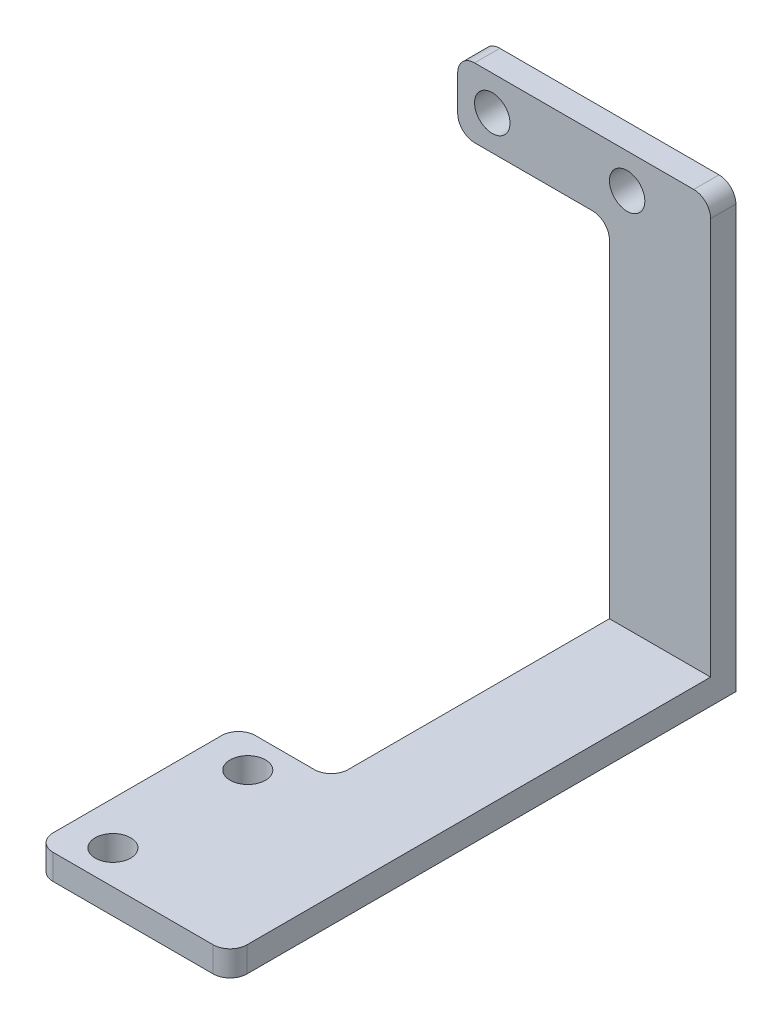
SolidWorks part; units mm, degrees
ref_plane "Front Plane" through (0, 0, 0) normal (0, 0, 1) x (1, 0, 0)
ref_plane "Top Plane" through (0, 0, 0) normal (0, 1, 0) x (1, 0, 0)
ref_plane "Right Plane" through (0, 0, 0) normal (1, 0, 0) x (0, 0, -1)
sketch "Sketch1" plane through (0, 0, 0) normal (0, 1, 0) x (1, 0, 0)
  line L0 (-17, -45) -> (6, -45) construction
  line L5 (-6, 0) -> (6, 0)
  line L6 (-6, 0) -> (-6, -33)
  line L8 (6, 0) -> (6, -57)
  line L9 (6, -57) -> (-17, -57)
  line L11 (-6, -33) -> (-17, -33)
  line L12 (-17, -57) -> (-17, -33)
  circle A4 centre (-11.9, -37) radius 2.1
  circle A5 centre (-11.9, -53) radius 2.1
  point P2 (0, 0)
  dimension "D2" = 4.2
  dimension "D1" = 24
  dimension "D3" = 16
  dimension "D4" = 3
  dimension "D5" = 11
  dimension "D6" = 12
  dimension "D7" = 45
extrude "Boss-Extrude1" add sketch "Sketch1" along normal blind 3
sketch "Sketch2" plane through (0, 0, 0) normal (0, 0, 1) x (1, 0, 0)
  line L0 (-11.9, 52.1) -> (-11.9, 43.9) construction
  line L1 (6, 0) -> (-6, 0)
  line L2 (6, 0) -> (6, 52.1)
  line L4 (-6, 0) -> (-6, 43.9)
  line L5 (6, 52.1) -> (-24, 52.1)
  line L7 (-6, 43.9) -> (-24, 43.9)
  line L8 (-24, 52.1) -> (-24, 43.9)
  line L11 (-17, 3) -> (6, 3) construction
  circle A0 centre (-19.9, 48) radius 2.1
  circle A1 centre (-3.9, 48) radius 2.1
  dimension "D1" = 4.2
  dimension "D2" = 16
  dimension "D4" = 2
  dimension "D5" = 2
  dimension "D6" = 2
  dimension "D3" = 45
extrude "Boss-Extrude2" add sketch "Sketch2" against normal blind 3
fillet "Fillet1" radius 2 8 edges at (-6, 1.5, 33) (6, 52.1, -1.5) (-24, 52.1, -1.5) (-24, 43.9, -1.5) (-6, 43.9, -1.5) (6, 1.5, 57) (-17, 1.5, 33) (-17, 1.5, 57)
equation "\"width\"= 24"
equation "\"thk\"= 3"
equation "\"holesize\"= 4.2"
equation "\"holedistance\"= ( 20 + 12 ) / 2"
equation "\"threaded_hole\"= 3.9"
equation "\"fillet_radius\"= 2"
equation "\"ground_clearance\"= 25"
equation "\"tire_thk\"= 4"
equation "\"innerwheel_diam\" = \"wheel_diam\"-2*\"tire_thk\""
equation "\"innerwheel_thk\"= 8"
equation "\"wheel_diam\"= 2*(\"width\"/2+\"ground_clearance\")"
equation "\"D1@Sketch1\"=\"width\""
equation "\"D2@Sketch1\"=\"holesize\""
equation "\"D3@Sketch1\"=\"holedistance\""
equation "\"D5@Sketch1\"=\"holedistance\"/2+3"
equation "\"D6@Sketch1\"=\"width\"/2"
equation "\"D1@Boss-Extrude1\"=\"thk\""
equation "\"D1@Sketch2\"=\"holesize\""
equation "\"D2@Sketch2\"=\"holedistance\""
equation "\"D5@Sketch2\"=\"D4@Sketch2\""
equation "\"D6@Sketch2\"=\"D4@Sketch2\""
equation "\"D1@Boss-Extrude2\"=\"thk\""
equation "\"D1@Fillet1\"=\"fillet_radius\""
equation "\"D3@Sketch2\"=42+\"thk\""
